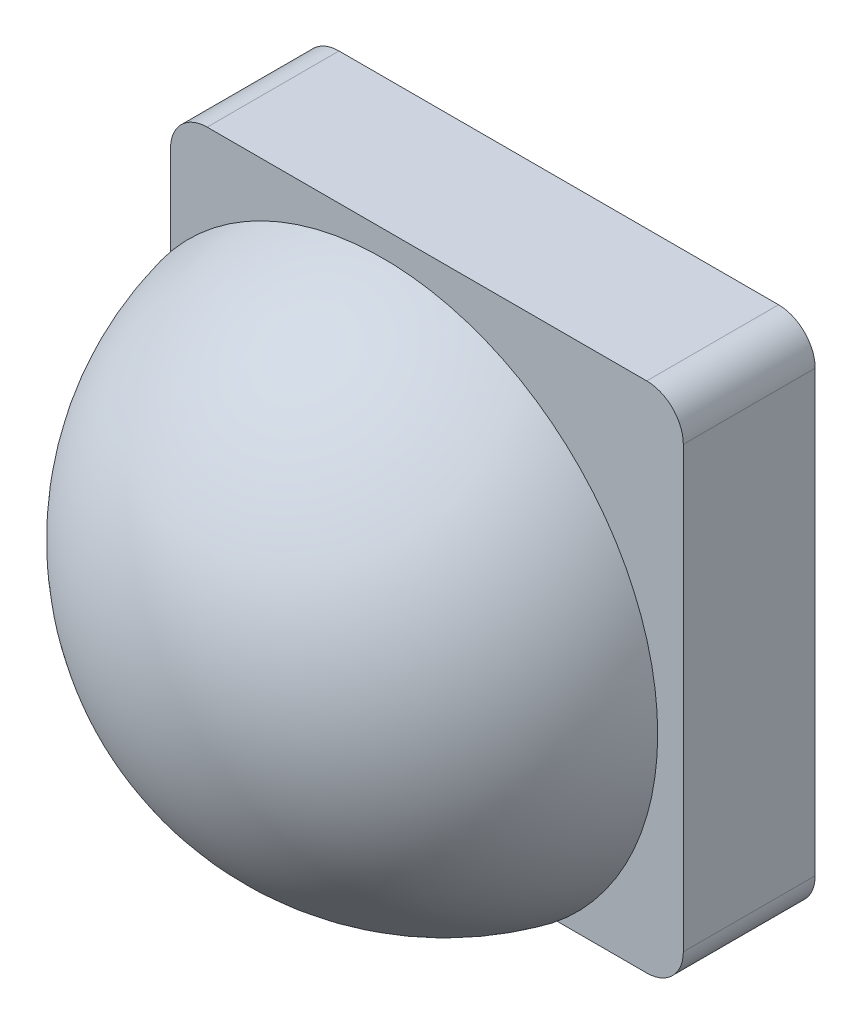
SolidWorks part; units mm, degrees
material "ABS"
ref_plane "Ebene vorne" through (0, 0, 0) normal (0, 0, 1) x (1, 0, 0)
ref_plane "Ebene oben" through (0, 0, 0) normal (0, 1, 0) x (1, 0, 0)
ref_plane "Ebene rechts" through (0, 0, 0) normal (1, 0, 0) x (0, 0, -1)
sketch "Skizze1" plane through (0, 0, 0) normal (0, 0, 1) x (1, 0, 0)
  line L8 (-30, -35) -> (30, -35)
  line L9 (35, -30) -> (35, 30)
  line L10 (30, 35) -> (-30, 35)
  line L11 (-35, 30) -> (-35, -30)
  line L12 (-30, -35) -> (30, -35)
  line L13 (35, -30) -> (35, 30)
  line L14 (30, 35) -> (-30, 35)
  line L15 (-35, 30) -> (-35, -30)
  arc A4 (-35, -30) -> (-30, -35) centre (-30, -30) ccw
  arc A5 (30, -35) -> (35, -30) centre (30, -30) ccw
  arc A6 (35, 30) -> (30, 35) centre (30, 30) ccw
  arc A7 (-30, 35) -> (-35, 30) centre (-30, 30) ccw
  arc A8 (-35, -30) -> (-30, -35) centre (-30, -30) ccw
  arc A9 (30, -35) -> (35, -30) centre (30, -30) ccw
  arc A10 (35, 30) -> (30, 35) centre (30, 30) ccw
  arc A11 (-30, 35) -> (-35, 30) centre (-30, 30) ccw
  dimension "D1" = 0
extrude "Aufsatz-Linear austragen1" add sketch "Skizze1" along normal blind 18
shell "Wandung1" thickness 2
sketch "Skizze2" plane through (0, 0, 18) normal (0, 0, 1) x (1, 0, 0)
  circle A0 centre (0, 0) radius 17.5
  dimension "D1" = 35
extrude "Aufsatz-Linear austragen2" add sketch "Skizze2" along normal blind 6
sketch "Skizze3" plane through (0, 0, 0) normal (0, 1, 0) x (1, 0, 0)
  line L0 (0, -24) -> (37.5, -24)
  line L1 (0, 8.7219) -> (0, -64.1491) construction
  line L2 (0, -24) -> (0, -54)
  line L3 (-17.5, -24) -> (17.5, -24) construction
  arc A0 (37.5, -24) -> (0, -54) centre (0, -15.5625) cw
  point P10 (0, 0)
  point P11 (0, -49.8754)
  dimension "D2" = 30
  dimension "D1" = 75
revolve "Rotation1" add sketch "Skizze3" angle 360 about L1
